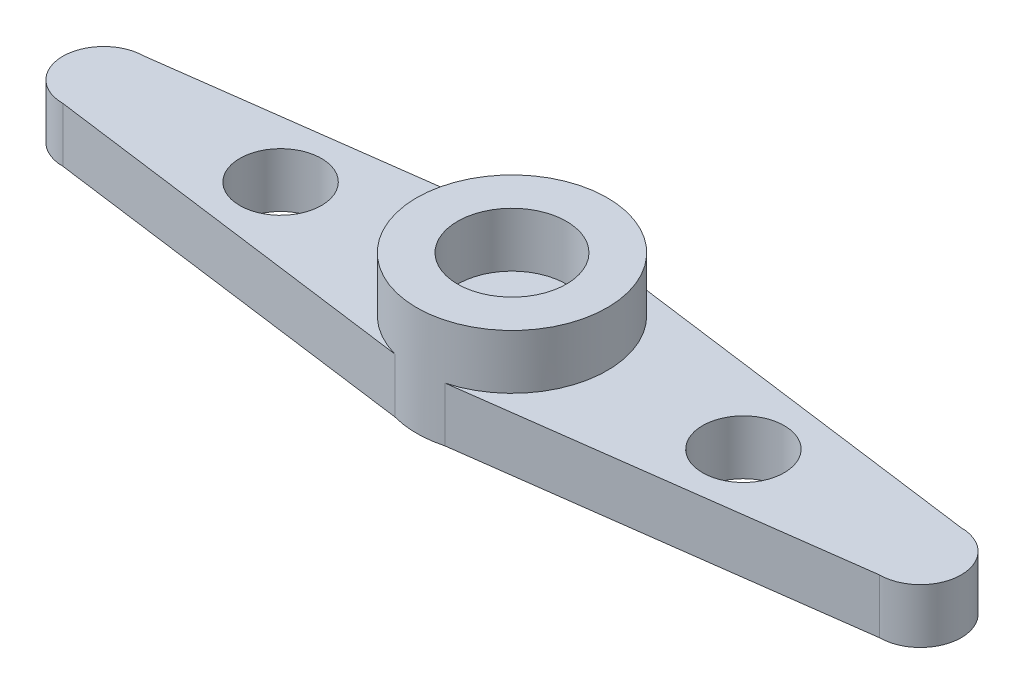
SolidWorks part; units mm, degrees
ref_plane "Plan de face" through (0, 0, 0) normal (0, 0, 1) x (1, 0, 0)
ref_plane "Plan de dessus" through (0, 0, 0) normal (0, 1, 0) x (1, 0, 0)
ref_plane "Plan de droite" through (0, 0, 0) normal (1, 0, 0) x (0, 0, -1)
sketch "Esquisse1" plane through (0, 0, 0) normal (0, 1, 0) x (1, 0, 0)
  circle A0 centre (0, 0) radius 3.5
  dimension "D1" = 7
extrude "Boss.-Extru.1" add sketch "Esquisse1" along normal blind 4
sketch "Esquisse2" plane through (0, 4, 0) normal (0, 1, 0) x (1, 0, 0)
  circle A0 centre (0, 0) radius 2
  dimension "D1" = 4
extrude "Enlèv. mat.-Extru.1" cut sketch "Esquisse2" against normal blind 2 contours A0
sketch "Esquisse3" plane through (0, 0, 0) normal (0, 1, 0) x (1, 0, 0)
  line L0 (0, 3.5) -> (15, 1.5)
  line L1 (15, 1.5) -> (15, -1.5)
  line L2 (15, -1.5) -> (0, -3.5)
  line L3 (0, -3.5) -> (0, 3.5)
  circle A0 centre (0, 0) radius 3.5 construction
  dimension "D1" = 15
  dimension "D2" = 3
  dimension "D3" = 2
extrude "Boss.-Extru.2" add sketch "Esquisse3" along normal blind 2
sketch "Esquisse4" plane through (0, 2, 0) normal (0, 1, 0) x (1, 0, 0)
  line L0 (15, -1.5) -> (15, 1.5) construction
  circle A0 centre (15, 0) radius 1.5
extrude "Boss.-Extru.3" add sketch "Esquisse4" against normal blind 2
mirror "Symétrie1" about plane through (0, 0, 0) normal (1, 0, 0) of "Boss.-Extru.3", "Boss.-Extru.2"
sketch "Esquisse5" plane through (0, 2, 0) normal (0, 1, 0) x (1, 0, 0)
  circle A0 centre (-8.5, 0) radius 1.5
  circle A1 centre (0, 0) radius 3.5 construction
  circle A2 centre (8.5, 0) radius 1.5
  circle A3 centre (0, 0) radius 2 construction
  dimension "D1" = 3
  dimension "D2" = 8.5
  dimension "D3" = 3
  dimension "D4" = 8.5
extrude "Enlèv. mat.-Extru.2" cut sketch "Esquisse5" against normal blind 2
